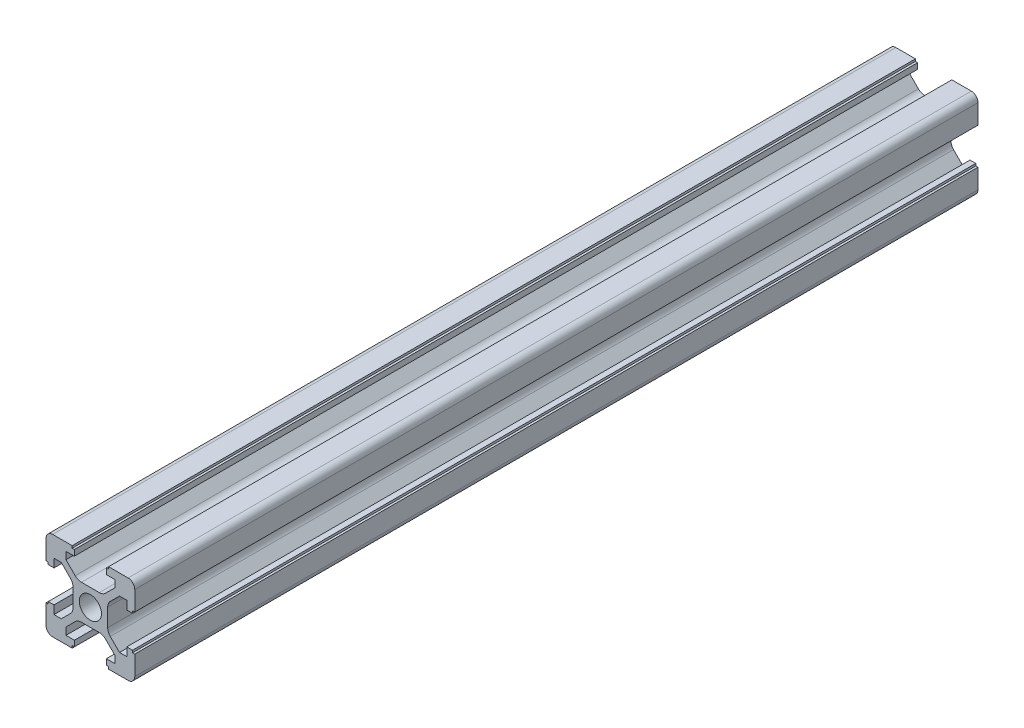
SolidWorks part; units mm, degrees
ref_plane "Front Plane" through (0, 0, 0) normal (0, 0, 1) x (1, 0, 0)
ref_plane "Top Plane" through (0, 0, 0) normal (0, 1, 0) x (1, 0, 0)
ref_plane "Right Plane" through (0, 0, 0) normal (1, 0, 0) x (0, 0, -1)
sketch "Sketch1" plane through (0, 0, 0) normal (0, 0, 1) x (1, 0, 0)
  line L0 (10, -4.1) -> (10, -8.5)
  line L1 (4.1, 10) -> (8.5, 10)
  line L2 (8.5, -10) -> (4.1, -10)
  line L3 (-8.5, -10) -> (-4.1, -10)
  line L4 (10, 8.5) -> (10, 4.1)
  line L7 (8.5, 10) -> (4.1, 10)
  line L8 (5.5, 6.5607) -> (3.4251, 4.4858)
  line L9 (8.5, 10) -> (4.1, 10)
  line L10 (3.9, 2.0109) -> (3.9, -2.0109)
  line L11 (2.0109, -3.9) -> (-2.0109, -3.9)
  line L12 (-3.9, -2.0109) -> (-3.9, 2.0109)
  line L13 (-2.0109, 3.9) -> (2.8393, 3.9)
  line L14 (2.5, 0) -> (22.2403, 0) construction
  line L15 (3.6, 9.5) -> (3.6, 8.2)
  line L16 (9.5, 3.6) -> (8.2, 3.6)
  line L17 (8.2, 3.6) -> (8.2, 5.5)
  line L18 (8.2, 5.5) -> (6.5607, 5.5)
  line L19 (10, -4.1) -> (10, -8.5)
  line L20 (4.1, 9.5) -> (3.6, 9.5)
  line L21 (4.1, 10) -> (4.1, 9.5)
  line L22 (8.5, 10) -> (4.1, 10)
  line L23 (10, 4.1) -> (9.5, 4.1)
  line L24 (9.5, 4.1) -> (9.5, 3.6)
  line L25 (5.5, 8.2) -> (5.5, 6.5607)
  line L26 (3.6, 8.2) -> (5.5, 8.2)
  line L27 (4.4858, 3.4251) -> (6.5607, 5.5)
  line L28 (10, -8.5) -> (10, -4.1)
  line L29 (6.5607, -5.5) -> (4.4858, -3.4251)
  line L30 (10, -8.5) -> (10, -4.1)
  line L31 (2.0109, -3.9) -> (-2.0109, -3.9)
  line L32 (3.9, 2.8393) -> (3.9, -2.0109)
  line L33 (9.5, -3.6) -> (8.2, -3.6)
  line L34 (3.6, -9.5) -> (3.6, -8.2)
  line L35 (3.6, -8.2) -> (5.5, -8.2)
  line L36 (5.5, -8.2) -> (5.5, -6.5607)
  line L37 (9.5, -4.1) -> (9.5, -3.6)
  line L38 (10, -4.1) -> (9.5, -4.1)
  line L39 (10, -8.5) -> (10, -4.1)
  line L40 (4.1, -10) -> (4.1, -9.5)
  line L41 (4.1, -9.5) -> (3.6, -9.5)
  line L42 (8.2, -5.5) -> (6.5607, -5.5)
  line L43 (8.2, -3.6) -> (8.2, -5.5)
  line L44 (3.4251, -4.4858) -> (5.5, -6.5607)
  line L45 (-4.1, -10) -> (-8.5, -10)
  line L46 (-10, -8.5) -> (-10, -4.1)
  line L47 (-8.5, -10) -> (-4.1, -10)
  line L48 (-5.5, -6.5607) -> (-3.4251, -4.4858)
  line L49 (-8.5, -10) -> (-4.1, -10)
  line L50 (-3.9, -2.0109) -> (-3.9, 2.0109)
  line L51 (2.0109, -3.9) -> (-2.0109, -3.9)
  line L52 (-3.6, -9.5) -> (-3.6, -8.2)
  line L53 (-9.5, -3.6) -> (-8.2, -3.6)
  line L54 (-8.2, -3.6) -> (-8.2, -5.5)
  line L55 (-8.2, -5.5) -> (-6.5607, -5.5)
  line L56 (-4.1, -9.5) -> (-3.6, -9.5)
  line L57 (-4.1, -10) -> (-4.1, -9.5)
  line L58 (-8.5, -10) -> (-4.1, -10)
  line L59 (-10, -4.1) -> (-9.5, -4.1)
  line L60 (-9.5, -4.1) -> (-9.5, -3.6)
  line L61 (-5.5, -8.2) -> (-5.5, -6.5607)
  line L62 (-3.6, -8.2) -> (-5.5, -8.2)
  line L63 (-4.4858, -3.4251) -> (-6.5607, -5.5)
  line L64 (-10, 4.1) -> (-10, 8.5)
  line L65 (-8.5, 10) -> (-4.1, 10)
  line L66 (-10, 8.5) -> (-10, 4.1)
  line L67 (-6.5607, 5.5) -> (-4.4858, 3.4251)
  line L68 (-10, 8.5) -> (-10, 4.1)
  line L69 (-2.0109, 3.9) -> (2.0109, 3.9)
  line L70 (-3.9, -2.0109) -> (-3.9, 2.0109)
  line L71 (-9.5, 3.6) -> (-8.2, 3.6)
  line L72 (-3.6, 9.5) -> (-3.6, 8.2)
  line L73 (-3.6, 8.2) -> (-5.5, 8.2)
  line L74 (-5.5, 8.2) -> (-5.5, 6.5607)
  line L75 (-9.5, 4.1) -> (-9.5, 3.6)
  line L76 (-10, 4.1) -> (-9.5, 4.1)
  line L77 (-10, 8.5) -> (-10, 4.1)
  line L78 (-4.1, 10) -> (-4.1, 9.5)
  line L79 (-4.1, 9.5) -> (-3.6, 9.5)
  line L80 (-8.2, 5.5) -> (-6.5607, 5.5)
  line L81 (-8.2, 3.6) -> (-8.2, 5.5)
  line L82 (-3.4251, 4.4858) -> (-5.5, 6.5607)
  line L83 (4.1, -10) -> (8.5, -10)
  arc A0 (2.0109, -3.9) -> (3.4251, -4.4858) centre (2.0109, -5.9) cw
  arc A1 (4.4858, -3.4251) -> (3.9, -2.0109) centre (5.9, -2.0109) cw
  arc A2 (3.9, 2.0109) -> (4.4858, 3.4251) centre (5.9, 2.0109) cw
  arc A3 (2.0109, 3.9) -> (3.4251, 4.4858) centre (2.0109, 5.9) ccw
  arc A4 (-2.0109, 3.9) -> (-3.4251, 4.4858) centre (-2.0109, 5.9) cw
  arc A5 (-4.4858, 3.4251) -> (-3.9, 2.0109) centre (-5.9, 2.0109) cw
  arc A6 (-3.4251, -4.4858) -> (-2.0109, -3.9) centre (-2.0109, -5.9) cw
  arc A7 (-3.9, -2.0109) -> (-4.4858, -3.4251) centre (-5.9, -2.0109) cw
  circle A8 centre (0, 0) radius 2.5
  arc A9 (-8.5, -10) -> (-10, -8.5) centre (-8.5, -8.5) cw
  arc A10 (-10, 8.5) -> (-8.5, 10) centre (-8.5, 8.5) cw
  arc A11 (8.5, 10) -> (10, 8.5) centre (8.5, 8.5) cw
  arc A12 (8.5, -10) -> (10, -8.5) centre (8.5, -8.5) ccw
  point P0 (0, 0)
  point P86 (0, 0)
  point P107 (10, -10)
  dimension "D3" = 2
  dimension "D5" = 5
  dimension "D2" = 1.5
  dimension "D8" = 1.5
  dimension "D4" = 6.1
  dimension "D6" = 4
  dimension "D11" = 0.5
  dimension "D12" = 0.5
extrude "Boss-Extrude2" add sketch "Sketch1" along normal blind 190
